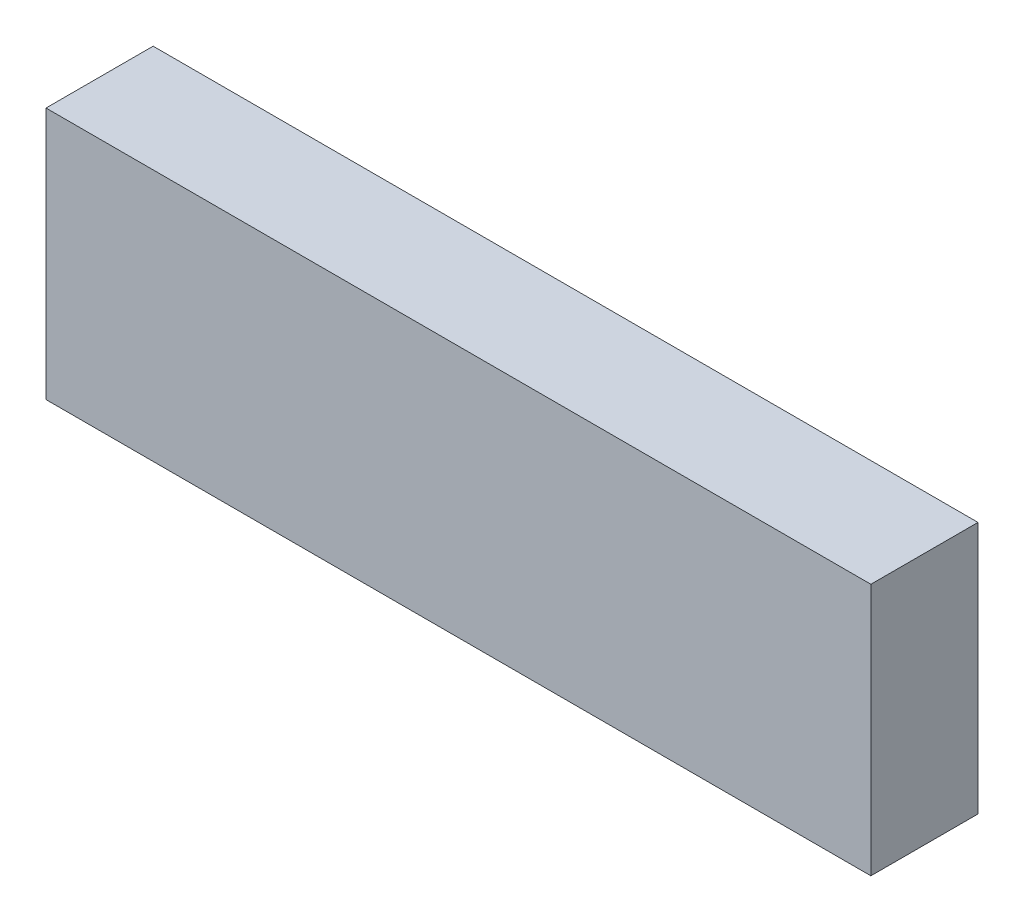
SolidWorks part; units mm, degrees
ref_plane "Front" through (0, 0, 0) normal (0, 0, 1) x (1, 0, 0)
ref_plane "Top" through (0, 0, 0) normal (0, 1, 0) x (1, 0, 0)
ref_plane "Right" through (0, 0, 0) normal (1, 0, 0) x (0, 0, -1)
sketch "Sketch1" plane through (0, 0, 0) normal (0, 0, 1) x (1, 0, 0)
  line L1 (68.453, -20.955) -> (-68.453, -20.955)
  line L2 (68.453, -20.955) -> (68.453, 20.955)
  line L3 (68.453, 20.955) -> (-68.453, 20.955)
  line L4 (-68.453, -20.955) -> (-68.453, 20.955)
  line L5 (68.453, -20.955) -> (-68.453, 20.955) construction
  line L6 (68.453, 20.955) -> (-68.453, -20.955) construction
  point P0 (0, 0)
  dimension "D1" = 41.91
  dimension "D2" = 136.906
extrude "Boss-Extrude1" add sketch "Sketch1" along normal blind 17.78
